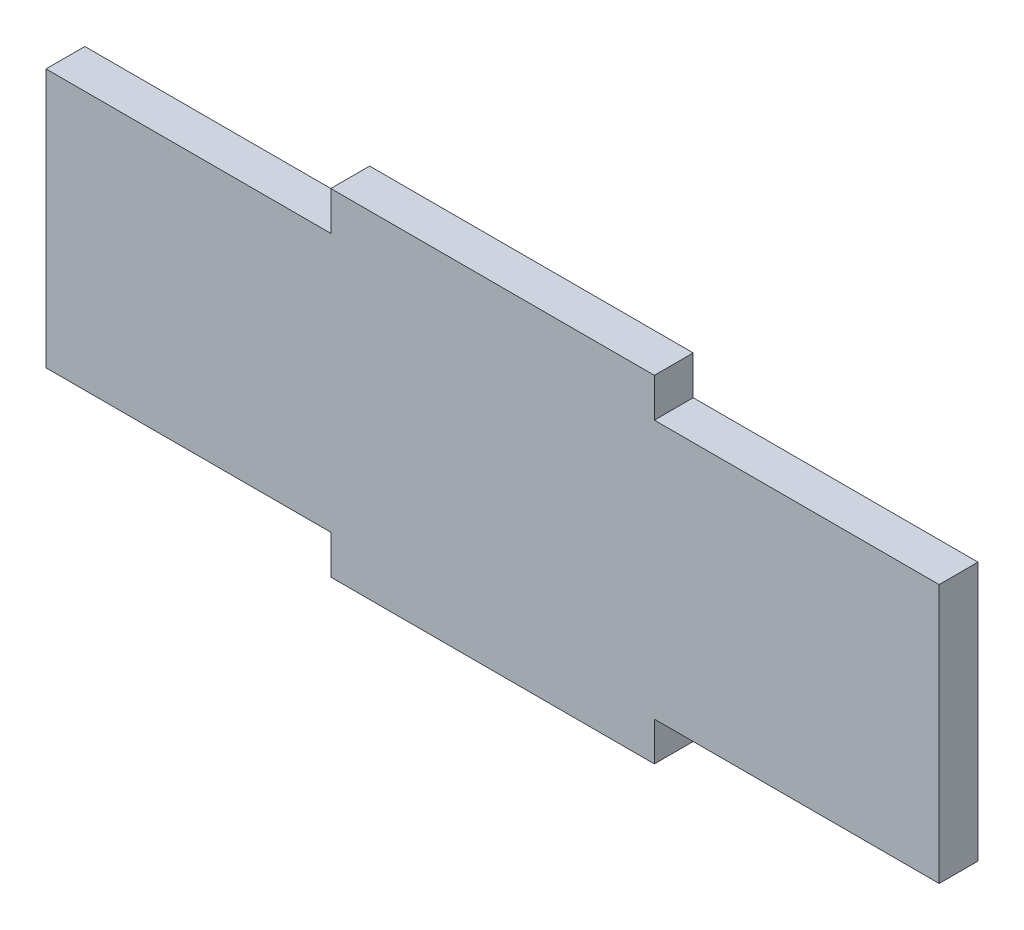
SolidWorks part; units mm, degrees
ref_plane "Plan de face" through (0, 0, 0) normal (0, 0, 1) x (1, 0, 0)
ref_plane "Plan de dessus" through (0, 0, 0) normal (0, 1, 0) x (1, 0, 0)
ref_plane "Plan de droite" through (0, 0, 0) normal (1, 0, 0) x (0, 0, -1)
sketch "Esquisse1" plane through (0, 0, 0) normal (0, 0, 1) x (1, 0, 0)
  line L1 (69, 20) -> (-69, 20)
  line L2 (69, 20) -> (69, -20)
  line L3 (69, -20) -> (-69, -20)
  line L4 (-69, 20) -> (-69, -20)
  line L5 (69, 20) -> (-69, -20) construction
  line L6 (69, -20) -> (-69, 20) construction
  point P0 (0, 0)
  dimension "D1" = 138
  dimension "D2" = 40
extrude "Boss.-Extru.1" add sketch "Esquisse1" along normal blind 6
sketch "Esquisse2" plane through (0, 0, 6) normal (0, 0, 1) x (1, 0, 0)
  line L0 (69, 20) -> (-69, 20) construction
  line L1 (-25, 20) -> (25, 20)
  line L2 (-25, 20) -> (-25, 26)
  line L3 (-25, 26) -> (25, 26)
  line L4 (25, 20) -> (25, 26)
  line L5 (-69, 20) -> (-69, -20) construction
  line L6 (-69, 0) -> (69, 0) construction
  line L7 (69, -20) -> (69, 20) construction
  line L8 (-25, -26) -> (25, -26)
  line L9 (25, -20) -> (25, -26)
  line L10 (-25, -20) -> (25, -20)
  line L11 (-25, -20) -> (-25, -26)
  dimension "D1" = 6
  dimension "D2" = 50
  dimension "D3" = 44
extrude "Boss.-Extru.2" add sketch "Esquisse2" against normal blind 6
